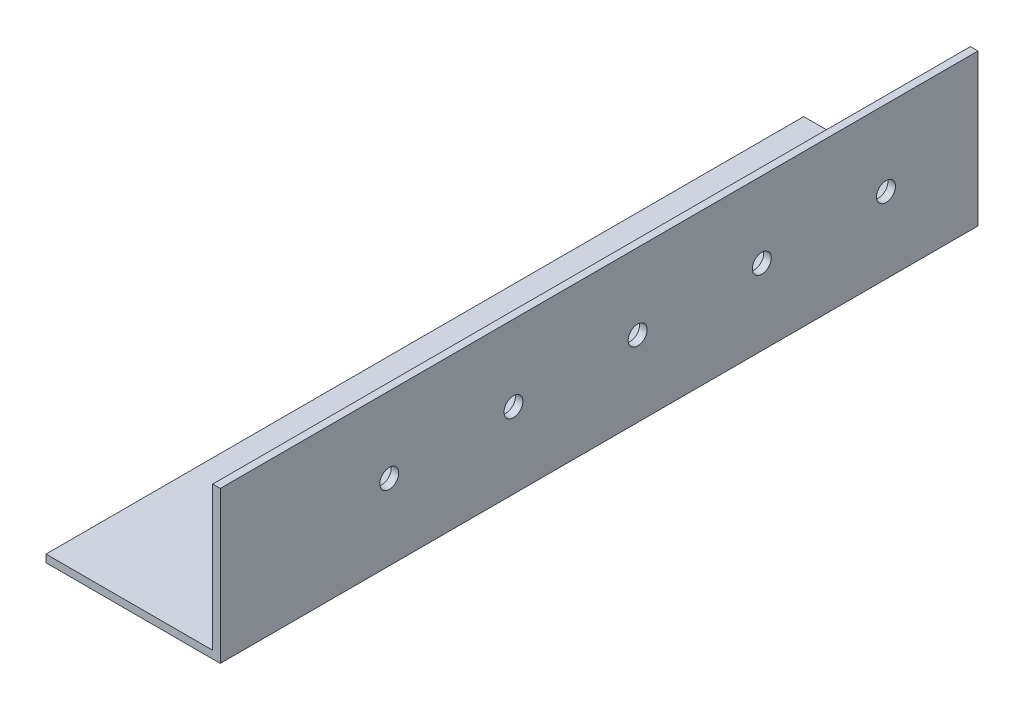
SolidWorks part; units mm, degrees
ref_plane "Alzado" through (0, 0, 0) normal (0, 0, 1) x (1, 0, 0)
ref_plane "Planta" through (0, 0, 0) normal (0, 1, 0) x (1, 0, 0)
ref_plane "Vista lateral" through (0, 0, 0) normal (1, 0, 0) x (0, 0, -1)
sketch "Croquis1" plane through (0, 0, 0) normal (0, 0, 1) x (1, 0, 0)
  line L0 (0, 22.9641) -> (0, -26.2672) construction
  line L1 (-27, -20) -> (27, -20) construction
  line L2 (-27, -20) -> (-27, 20) construction
  line L3 (-27, 20) -> (27, 20) construction
  line L4 (27, -20) -> (27, 20) construction
  line L5 (-27, -20) -> (27, 20) construction
  line L6 (-27, 20) -> (27, -20) construction
  line L7 (-27, 20) -> (-27, -20)
  line L8 (-27, -20) -> (27, -20)
  line L9 (0, -20) -> (0, -18)
  line L10 (25, -18) -> (-25, -18)
  line L11 (-25, -18) -> (-25, 20)
  line L12 (-25, 20) -> (-27, 20)
  line L13 (25, -18) -> (25, 20)
  line L14 (27, 20) -> (27, -20)
  line L15 (25, 20) -> (27, 20)
  point P0 (0, 0)
  dimension "D1" = 40
  dimension "D2" = 54
  dimension "D3" = 2
  dimension "D4" = 2
extrude "Saliente-Extruir1" add sketch "Croquis1" along normal mid plane 200 contours L11 L12 L7 L8 L9 L10
sketch "Croquis2" plane through (27, 0, 0) normal (1, 0, 0) x (0, 0, -1)
  line L0 (0, 0) -> (-56.8754, 0) construction
  line L1 (10.16, 0) -> (86.0635, 0) construction
  circle A0 centre (-55.4, 0) radius 2.5
  circle A1 centre (-22.62, 0) radius 2.5
  circle A2 centre (10.16, 0) radius 2.5
  circle A3 centre (42.94, 0) radius 2.5
  circle A4 centre (75.72, 0) radius 2.5
  point P13 (75.72, 0)
  point P16 (69.9483, 0)
  point P17 (0, 0)
  dimension "D2" = 5
  dimension "D6" = 32.78
  dimension "D1" = 55.4
  dimension "D3" = 32.78
  dimension "D4" = 32.78
  dimension "D5" = 32.78
extrude "Cortar-Extruir1" cut sketch "Croquis2" against normal blind 10
sketch "Croquis3" plane through (0, 0, 100) normal (0, 0, 1) x (1, 0, 0)
  line L0 (-25, 20) -> (-27, 20) construction
  line L1 (-27, -20) -> (-19, -20)
  line L2 (-27, -20) -> (-27, 20)
  line L3 (-27, 20) -> (-19, 20)
  line L4 (-19, -20) -> (-19, 20)
  dimension "D1" = 8
extrude "Cortar-Extruir2" cut sketch "Croquis3" against normal through all
